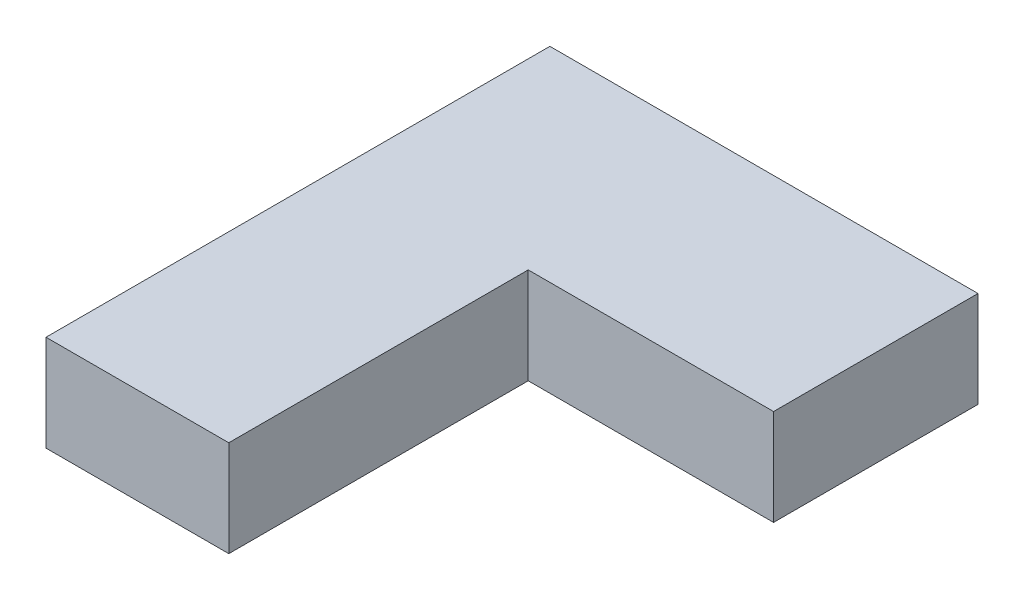
SolidWorks part; units mm, degrees
ref_plane "Front Plane" through (0, 0, 0) normal (0, 0, 1) x (1, 0, 0)
ref_plane "Top Plane" through (0, 0, 0) normal (0, 1, 0) x (1, 0, 0)
ref_plane "Right Plane" through (0, 0, 0) normal (1, 0, 0) x (0, 0, -1)
sketch "Sketch1" plane through (0, 0, 0) normal (0, 1, 0) x (1, 0, 0)
  line L0 (0, 0) -> (0, 52.4562)
  line L1 (0, 52.4562) -> (44.569, 52.4562)
  line L2 (44.569, 52.4562) -> (44.569, 31.1733)
  line L3 (44.569, 31.1733) -> (19.0295, 31.1733)
  line L4 (19.0295, 31.1733) -> (19.0295, 0)
  line L5 (19.0295, 0) -> (0, 0)
extrude "Boss-Extrude1" add sketch "Sketch1" along normal blind 10
